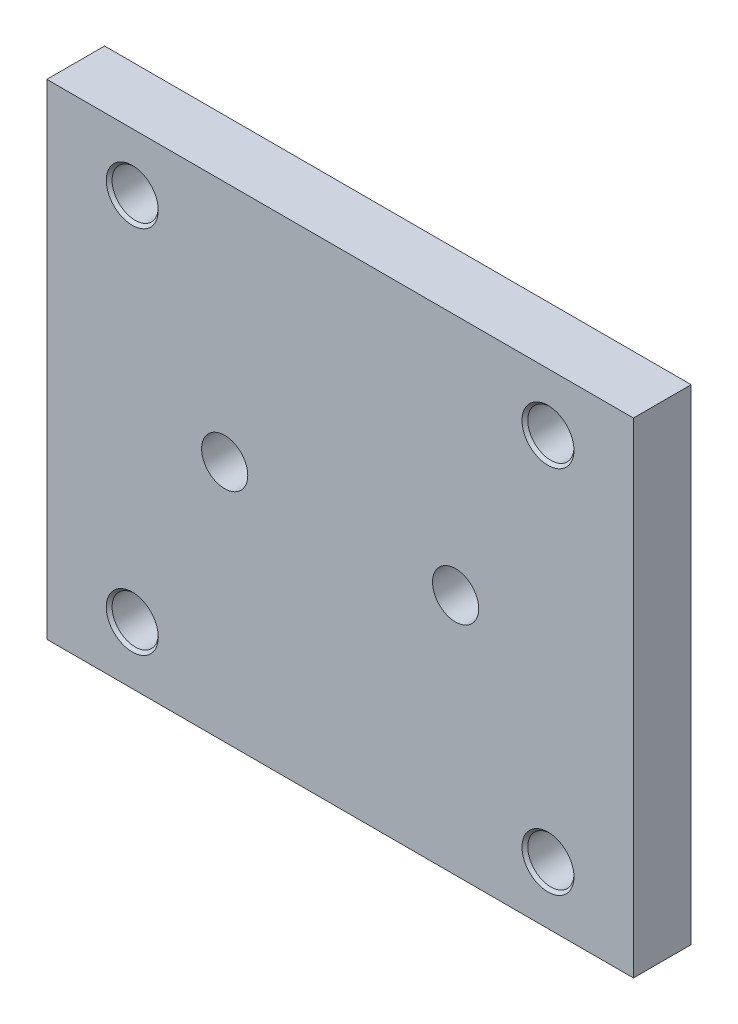
SolidWorks part; units mm, degrees
ref_plane "Front Plane" through (0, 0, 0) normal (0, 0, 1) x (1, 0, 0)
ref_plane "Top Plane" through (0, 0, 0) normal (0, 1, 0) x (1, 0, 0)
ref_plane "Right Plane" through (0, 0, 0) normal (1, 0, 0) x (0, 0, -1)
sketch "Sketch1" plane through (0, 0, 0) normal (0, 0, 1) x (1, 0, 0)
  line L0 (-127, 105) -> (127, 105)
  line L1 (-127, 105) -> (-127, -105)
  line L2 (-127, -105) -> (127, -105)
  line L3 (127, 105) -> (127, -105)
  circle A0 centre (-90, 80) radius 10
  circle A1 centre (90, 80) radius 10
  circle A2 centre (90, -80) radius 10
  circle A3 centre (-90, -80) radius 10
extrude "Boss-Extrude1" add sketch "Sketch1" along normal blind 25
sketch "Sketch2" plane through (0, 0, 25) normal (0, 0, 1) x (1, 0, 0)
  line L3 (-50, -105) -> (50, -105)
  circle A0 centre (-50, 0) radius 10
  circle A1 centre (50, 0) radius 10
  point P0 (0, 0)
  point P6 (0, 0)
  dimension "D2" = 20
extrude "Cut-Extrude1" cut sketch "Sketch2" against normal up to next contours A0 | A1
sketch "Sketch3" plane through (0, 0, 25) normal (0, 0, 1) x (1, 0, 0)
  circle A0 centre (-90, 80) radius 11.25
  circle A1 centre (90, 80) radius 11.25
  circle A2 centre (90, -80) radius 11.25
  circle A3 centre (-90, -80) radius 11.25
  dimension "D1" = 22.5
extrude "Cut-Extrude2" cut sketch "Sketch3" against normal blind 25 draft 45
